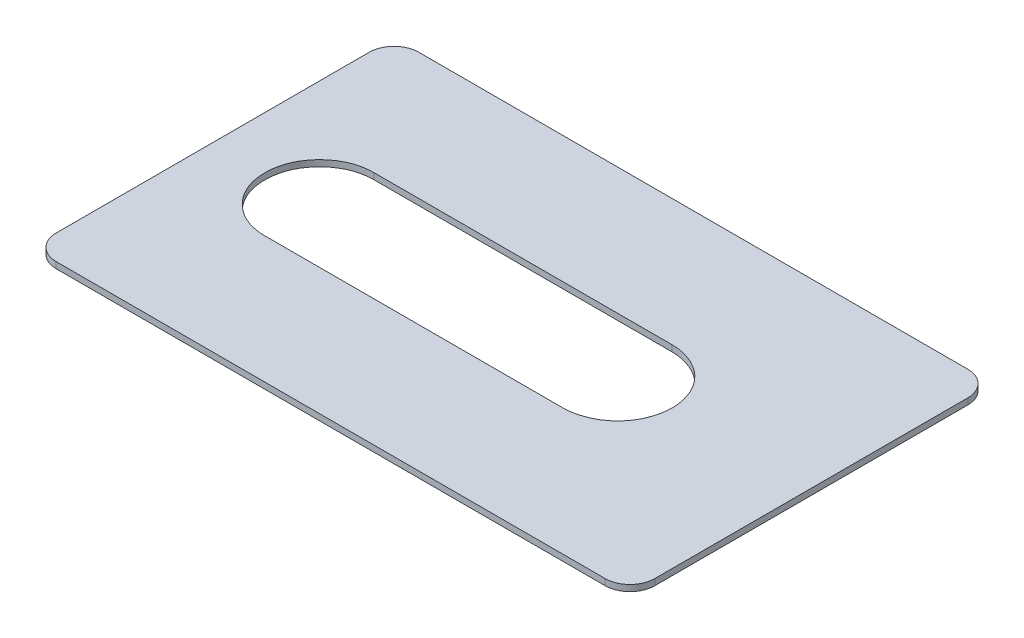
SolidWorks part; units mm, degrees
material "SANTOPRENE"
ref_plane "Front Plane" through (0, 0, 0) normal (0, 0, 1) x (1, 0, 0)
ref_plane "Top Plane" through (0, 0, 0) normal (0, 1, 0) x (1, 0, 0)
ref_plane "Right Plane" through (0, 0, 0) normal (1, 0, 0) x (0, 0, -1)
sketch "Sketch1" plane through (0, 0, 0) normal (0, 1, 0) x (1, 0, 0)
  line L0 (6, -2) -> (-6, -2) construction
  line L1 (-6, 2) -> (6, 2) construction
  line L2 (-10.5004, -7.5) -> (13.9996, -7.5) construction
  line L3 (13.9996, -7.5) -> (13.9996, 7.5) construction
  line L4 (13.9996, 7.5) -> (-10.5004, 7.5) construction
  line L5 (-10.5004, 7.5) -> (-10.5004, -7.5) construction
  line L6 (-6, 2.2) -> (6, 2.2)
  line L7 (6, -2.2) -> (-6, -2.2)
  line L8 (12.7996, 7.3) -> (-9.3004, 7.3)
  line L9 (-10.3004, 6.3) -> (-10.3004, -6.3)
  line L10 (-9.3004, -7.3) -> (12.7996, -7.3)
  line L11 (13.7996, -6.3) -> (13.7996, 6.3)
  line L12 (13.7996, 7.3) -> (-10.3004, 7.3) construction
  line L13 (13.7996, -7.3) -> (13.7996, 7.3) construction
  line L14 (-10.3004, -7.3) -> (13.7996, -7.3) construction
  line L15 (-10.3004, 7.3) -> (-10.3004, -7.3) construction
  arc A0 (12.7996, 7.3) -> (13.7996, 6.3) centre (12.7996, 6.3) cw
  arc A1 (12.7996, -7.3) -> (13.7996, -6.3) centre (12.7996, -6.3) ccw
  arc A2 (-10.3004, -6.3) -> (-9.3004, -7.3) centre (-9.3004, -6.3) ccw
  arc A3 (-9.3004, 7.3) -> (-10.3004, 6.3) centre (-9.3004, 6.3) ccw
  spline S0 degree 2 poles (-6, -2) (-6.8289, -2) (-7.4142, -1.4142) (-8.0004, -0.8275) (-8, 0) (-7.9996, 0.8293) (-7.4142, 1.4142) (-6.8279, 2) (-6, 2) knots 0 0 0 0.25 0.25 0.5 0.5 0.75 0.75 1 1 1 construction
  spline S1 degree 2 poles (6, 2) (6.3982, 2) (6.7654, 1.8478) (7.1335, 1.6951) (7.4142, 1.4142) (7.6959, 1.1323) (7.8478, 0.7654) (8.0001, 0.3971) (8, 0) (7.9999, -0.3986) (7.8478, -0.7654) (7.6951, -1.1335) (7.4142, -1.4142) (7.1323, -1.6959) (6.7654, -1.8478) (6.3974, -2) (6, -2) knots 0 0 0 0.125 0.125 0.25 0.25 0.375 0.375 0.5 0.5 0.625 0.625 0.75 0.75 0.875 0.875 1 1 1 construction
  spline S2 degree 1 poles (-6, -2.2) (-6, 2.2) knots 0 0 1 1 construction
  spline S3 degree 1 poles (6, 2.2) (6, -2.2) knots 0 0 1 1 construction
  spline S4 degree 3 poles (-6, -2.2) (-6.2866, -2.2) (-6.8702, -2.0965) (-7.5918, -1.5923) (-8.0969, -0.8677) (-8.2517, -0.0002) (-8.0963, 0.8691) (-7.592, 1.5921) (-6.8693, 2.0965) (-6.2865, 2.2) (-6, 2.2) knots 0 0 0 0 0.125 0.25 0.375 0.5 0.625 0.75 0.875 1 1 1 1
  spline S5 degree 3 poles (6, 2.2) (6.5613, 2.2) (7.7307, 1.7239) (8.4347, -0.0001) (7.7306, -1.724) (6.5612, -2.2) (6, -2.2) knots 0 0 0 0 0.25 0.5 0.75 1 1 1 1
  point P29 (0, 2)
  dimension "D3" = 1
  dimension "D1" = 0.2
  dimension "D2" = 0.2
  dimension "D4" = 12
  dimension "D5" = 4
  dimension "D6" = 12
  dimension "D7" = 15
  dimension "D8" = 24.5
  dimension "D9" = 5.1
  dimension "D10" = 4.3004
  dimension "D11" = 2
extrude "Boss-Extrude1" add sketch "Sketch1" along normal blind 0.25
